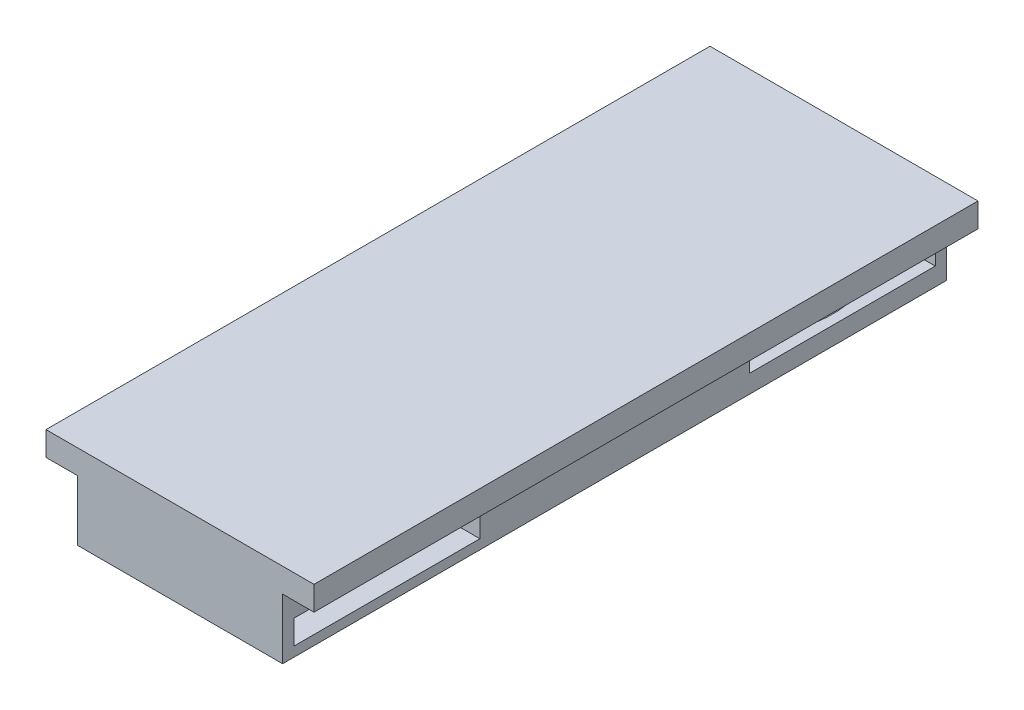
SolidWorks part; units mm, degrees
ref_plane "Front Plane" through (0, 0, 0) normal (0, 0, 1) x (1, 0, 0)
ref_plane "Top Plane" through (0, 0, 0) normal (0, 1, 0) x (1, 0, 0)
ref_plane "Right Plane" through (0, 0, 0) normal (1, 0, 0) x (0, 0, -1)
sketch "Sketch2" plane through (0, 0, 0) normal (0, 0, 1) x (1, 0, 0)
  line L0 (2.6, -1.7808) -> (19.6, -1.7808)
  line L1 (2.6, -1.7808) -> (2.6, 3.2192)
  line L2 (19.6, -1.7808) -> (19.6, 3.2192)
  line L3 (2.6, 3.2192) -> (0, 3.2192)
  line L4 (0, 3.2192) -> (0, 5.2192)
  line L5 (22.2, 5.2192) -> (22.2, 3.2192)
  line L6 (22.2, 3.2192) -> (19.6, 3.2192)
  line L7 (0, 5.2192) -> (22.2, 5.2192)
  line L8 (0, -55) -> (0, 55) construction
  dimension "D1" = 2
  dimension "D2" = 2
  dimension "D3" = 17
  dimension "D4" = 5
  dimension "D5" = 2.6
  dimension "D6" = 2.6
extrude "Boss-Extrude1" add sketch "Sketch2" against normal blind 55
sketch "Sketch3" plane through (0, -1.7808, 0) normal (0, -1, 0) x (1, 0, 0)
  line L0 (11.1, -46.36) -> (11.1, -54.832) construction
  line L5 (2.6, -27.5) -> (11.1, -27.5) construction
  line L6 (11.1, -8.64) -> (11.1, -46.36) construction
  line L11 (55, 0) -> (-55, 0) construction
  line L12 (2.6, -55) -> (19.6, -55) construction
  line L14 (19.6, -55) -> (19.6, 0) construction
  line L15 (2.6, -55) -> (2.6, 0) construction
  circle A2 centre (11.1, -8.64) radius 7.7
  circle A3 centre (11.1, -46.36) radius 7.7
  point P2 (0, 0)
  point P10 (12.1802, -55)
  point P14 (11.1, -27.5)
  point P16 (0, 0)
  dimension "D1" = 15.4
  dimension "D2" = 15.4
  dimension "D3" = 8.64
  dimension "D4" = 46.36
  dimension "D5" = 8.472
  dimension "D6" = 8.64
  dimension "D7" = 8.5
  dimension "D8" = 8.5
extrude "Cut-Extrude1" cut sketch "Sketch3" against normal blind 2.8
sketch "Sketch4" plane through (0, -1.7808, 0) normal (0, -1, 0) x (1, 0, 0)
  circle A0 centre (11.1, -8.64) radius 7.7
  circle A1 centre (11.1, -46.36) radius 7.7
  circle A2 centre (11.1, -8.64) radius 5.5
  circle A3 centre (11.1, -46.36) radius 5.5
  dimension "D1" = 11
  dimension "D2" = 11
extrude "Boss-Extrude2" add sketch "Sketch4" against normal blind 0.8
sketch "Sketch5" plane through (19.6, 0, 0) normal (1, 0, 0) x (0, 0, -1)
  line L1 (0.94, 1.0192) -> (16.34, 1.0192)
  line L2 (0.94, 1.0192) -> (0.94, -0.9808)
  line L3 (0.94, -0.9808) -> (16.34, -0.9808)
  line L4 (16.34, 1.0192) -> (16.34, -0.9808)
  line L5 (38.66, 1.7192) -> (54.06, 1.7192)
  line L6 (38.66, 1.7192) -> (38.66, -0.2808)
  line L7 (38.66, -0.2808) -> (54.06, -0.2808)
  line L8 (54.06, 1.7192) -> (54.06, -0.2808)
  line L10 (55, -1.7808) -> (0, -1.7808) construction
  line L11 (0.94, 1.0192) -> (0.94, -0.9808) construction
  line L12 (54.06, -0.9808) -> (54.06, 1.0192) construction
  dimension "D1" = 0
  dimension "D2" = 0
  dimension "D3" = 15.4
  dimension "D4" = 15.4
  dimension "D5" = 0.8
  dimension "D6" = 1.5
  dimension "D7" = 2
  dimension "D8" = 2
extrude "Cut-Extrude2" cut sketch "Sketch5" against normal blind 8.5
